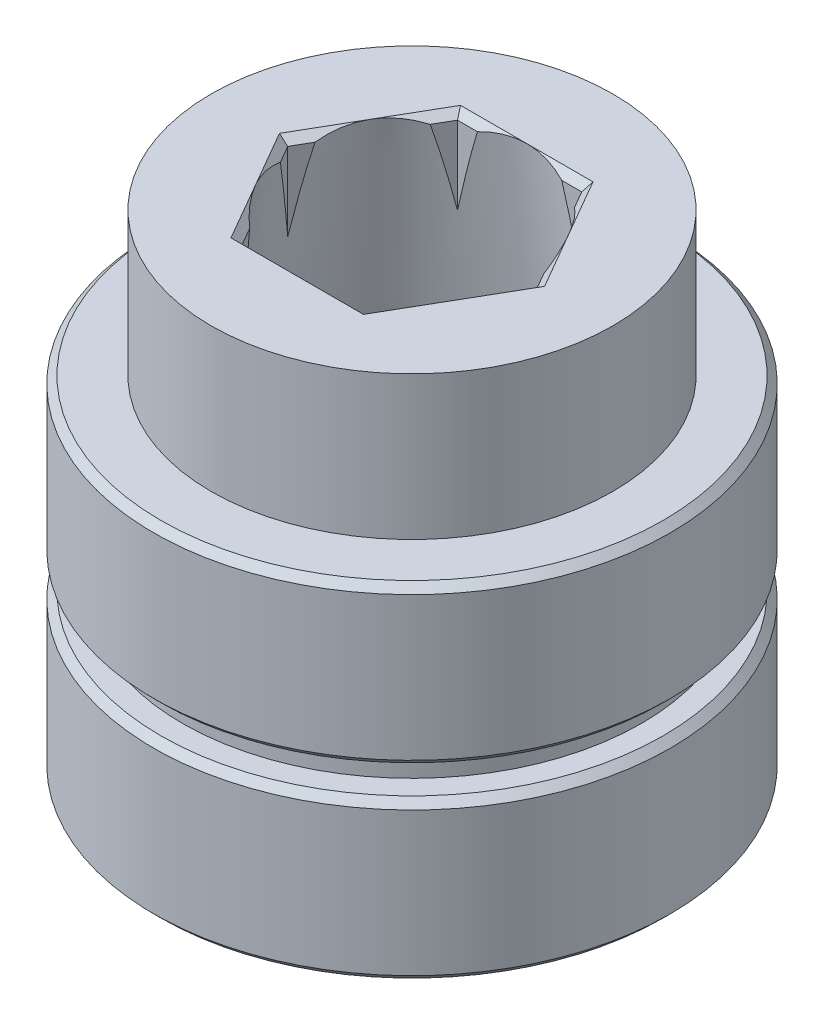
SolidWorks part; units mm, degrees
ref_plane "Ebene vorne" through (0, 0, 0) normal (0, 0, 1) x (1, 0, 0)
ref_plane "Ebene oben" through (0, 0, 0) normal (0, 1, 0) x (1, 0, 0)
ref_plane "Ebene rechts" through (0, 0, 0) normal (1, 0, 0) x (0, 0, -1)
sketch "Skizze1" plane through (0, 0, 0) normal (0, 0, 1) x (1, 0, 0)
  line L0 (0, -292.4333) -> (0, 14329.2307) construction
  line L2 (0, 0) -> (9, 0)
  line L3 (0, 0) -> (0, 5.5)
  line L4 (8, 5.5) -> (9, 5.5)
  line L5 (9, 0) -> (9, 5.5)
  line L7 (0, 5.5) -> (0, 6.5)
  line L9 (8, 5.5) -> (8, 6.5)
  line L10 (8, 6.5) -> (9, 6.5)
  line L11 (0, 6.5) -> (0, 12)
  line L12 (7, 12) -> (9, 12)
  line L13 (9, 6.5) -> (9, 12)
  line L15 (0, 12) -> (0, 17)
  line L16 (0, 17) -> (7, 17)
  line L17 (7, 12) -> (7, 17)
  dimension "D1" = 9
  dimension "D2" = 8
  dimension "D3" = 1
  dimension "D4" = 9
  dimension "D5" = 5.5
  dimension "D6" = 5.5
  dimension "D7" = 7
  dimension "D8" = 5
  dimension "D9" = 5.5
  dimension "D10" = 6.5
  dimension "D11" = 12
revolve "Rotation1" add sketch "Skizze1" angle 360 about L0
chamfer "Fase1" distance 0.25 angle 45 4 edges at (9, 0, 0) (9, 5.5, 0) (9, 12, 0) (9, 6.5, 0)
ref_plane "Ebene1" through (0, 17, 0) normal (0, 1, 0) x (1, 0, 0)
sketch "Skizze2" plane through (0, 17, 0) normal (0, 1, 0) x (1, 0, 0)
  line L1 (2.1651, -3.75) -> (4.3301, 0)
  line L2 (4.3301, 0) -> (2.1651, 3.75)
  line L3 (2.1651, 3.75) -> (-2.1651, 3.75)
  line L4 (-2.1651, 3.75) -> (-4.3301, 0)
  line L5 (-4.3301, 0) -> (-2.1651, -3.75)
  line L6 (-2.1651, -3.75) -> (2.1651, -3.75)
  circle A0 centre (0, 0) radius 3.75 construction
  dimension "D1" = 7.5
extrude "Schnitt-Linear austragen1" cut sketch "Skizze2" against normal through all
chamfer "Fase2" distance 0.25 angle 45 6 edges at (0, 17, 3.75) (3.2476, 17, 1.875) (3.2476, 17, -1.875) (0, 17, -3.75) (-3.2476, 17, -1.875) (-3.2476, 17, 1.875)
sketch "Skizze3" plane through (0, 0, 0) normal (0, 1, 0) x (1, 0, 0)
  circle A0 centre (0, 0) radius 7.5
  dimension "D1" = 15
extrude "Schnitt-Linear austragen2" cut sketch "Skizze3" along normal blind 10
sketch "Skizze4" plane through (0, 0, 0) normal (0, 1, 0) x (1, 0, 0)
  circle A0 centre (0, 0) radius 5.8901
sketch "Skizze5" plane through (0, 17, 0) normal (0, 1, 0) x (1, 0, 0)
  circle A0 centre (0, 0) radius 4
  dimension "D1" = 8
loft "Schnitt-Ausformung2" cut profiles "Skizze5", "Skizze4"
